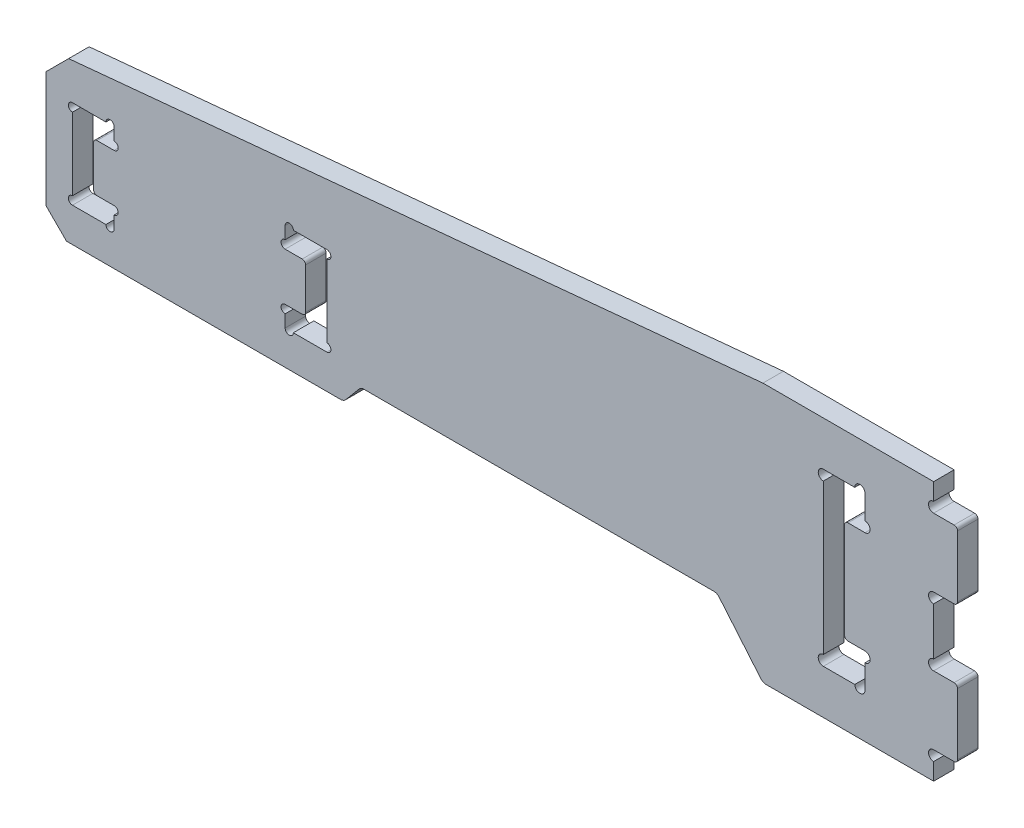
SolidWorks part; units mm, degrees
ref_plane "前视基准面" through (0, 0, 0) normal (0, 0, 1) x (1, 0, 0)
ref_plane "上视基准面" through (0, 0, 0) normal (0, 1, 0) x (1, 0, 0)
ref_plane "右视基准面" through (0, 0, 0) normal (1, 0, 0) x (0, 0, -1)
sketch "草图1" plane through (0, 0, 0) normal (0, 0, 1) x (1, 0, 0)
  line L1 (65, -19) -> (-65, -19)
  line L2 (65, -19) -> (65, 19)
  line L3 (65, 19) -> (-65, 19)
  line L4 (-65, -19) -> (-65, 19)
  line L5 (65, -19) -> (-65, 19) construction
  line L6 (65, 19) -> (-65, -19) construction
  point P0 (0, 0)
  dimension "D1" = 130
  dimension "D2" = 38
extrude "凸台-拉伸1" add sketch "草图1" along normal mid plane 3
sketch "草图2" plane through (0, 0, 1.5) normal (0, 0, 1) x (1, 0, 0)
  line L0 (65, -19) -> (65, 19) construction
  line L1 (68.5, 5) -> (65, 5)
  line L2 (68.5, 5) -> (68.5, 15)
  line L3 (68.5, 15) -> (65, 15)
  line L4 (65, 5) -> (65, 15)
  line L5 (68.5, 5) -> (65, 15) construction
  line L6 (68.5, 15) -> (65, 5) construction
  line L7 (66.75, 10) -> (66.75, -10) construction
  line L8 (68.5, -15) -> (65, -15)
  line L9 (68.5, -15) -> (68.5, -5)
  line L10 (68.5, -5) -> (65, -5)
  line L11 (65, -15) -> (65, -5)
  line L12 (68.5, -15) -> (65, -5) construction
  line L13 (68.5, -5) -> (65, -15) construction
  point P0 (66.75, 10)
  point P7 (66.75, -10)
  point P14 (66.75, 0)
  dimension "D1" = 20
  dimension "D2" = 3.5
  dimension "D3" = 10
extrude "凸台-拉伸2" add sketch "草图2" against normal blind 3
sketch "草图4" plane through (0, 0, 1.5) normal (0, 0, 1) x (1, 0, 0)
  line L0 (48.85, 12.5) -> (54.95, 12.5)
  line L1 (54.95, 12.5) -> (54.95, 7.5)
  line L2 (54.95, 7.5) -> (51.95, 7.5)
  line L3 (51.95, 7.5) -> (51.95, -7.5)
  line L4 (51.95, -7.5) -> (54.95, -7.5)
  line L5 (54.95, -7.5) -> (54.95, -12.5)
  line L6 (54.95, -12.5) -> (48.85, -12.5)
  line L7 (48.85, -12.5) -> (48.85, 12.5)
  line L9 (65, 15) -> (65, 19) construction
  point P8 (48.85, 0)
  dimension "D1" = 15
  dimension "D2" = 10.05
  dimension "D3" = 3
  dimension "D4" = 3.1
  dimension "D5" = 5
extrude "切除-拉伸2" cut sketch "草图4" against normal through all
sketch "草图3" plane through (0, 0, 1.5) normal (0, 0, 1) x (1, 0, 0)
  line L0 (65, 15) -> (65, 19) construction
  line L1 (65, -5) -> (65, 5) construction
  line L2 (65, -19) -> (65, -15) construction
  line L3 (54.95, 7.5) -> (54.95, 12.5) construction
  line L4 (54.95, 12.5) -> (48.85, 12.5) construction
  line L5 (48.85, 12.5) -> (48.85, -12.5) construction
  line L6 (54.95, -12.5) -> (54.95, -7.5) construction
  line L7 (48.85, -12.5) -> (54.95, -12.5) construction
  circle A0 centre (65, 15.75) radius 0.75
  circle A1 centre (65, 4.25) radius 0.75
  circle A2 centre (65, -4.25) radius 0.75
  circle A3 centre (65, -15.75) radius 0.75
  circle A4 centre (54.95, 8.25) radius 0.75
  circle A5 centre (54.2, 12.5) radius 0.75
  circle A6 centre (48.85, 11.75) radius 0.75
  circle A7 centre (48.85, -11.75) radius 0.75
  circle A8 centre (54.95, -8.25) radius 0.75
  circle A9 centre (54.2, -12.5) radius 0.75
  dimension "D1" = 1.5
extrude "切除-拉伸1" cut sketch "草图3" against normal through all
fillet "圆角1" radius 0.5 6 edges at (68.5, -5, 0) (68.5, -15, 0) (68.5, 15, 0) (68.5, 5, 0) (51.95, -7.5, 0) (51.95, 7.5, 0)
sketch "草图5" plane through (0, 0, 1.5) normal (0, 0, 1) x (1, 0, 0)
  line L1 (-65, 19) -> (-65, -19) construction
  line L6 (-65, -19) -> (-65, -14)
  line L7 (-65, -14) -> (35.8045, -14)
  line L8 (35.8045, -14) -> (40, -19)
  line L9 (-65, -19) -> (65, -19) construction
  line L10 (40, -19) -> (-65, -19)
  dimension "D4" = 5
  dimension "D5" = 105
  dimension "D6" = 50
extrude "切除-拉伸3" cut sketch "草图5" against normal through all
fillet "圆角2" radius 1 2 edges at (40, -19, 0) (35.8045, -14, 0)
sketch "草图6" plane through (0, 0, 1.5) normal (0, 0, 1) x (1, 0, 0)
  line L0 (-65, 9) -> (40, 19)
  line L1 (-65, 19) -> (-65, -14) construction
  line L2 (40, 19) -> (-65, 19)
  line L3 (-65, 19) -> (-65, 9)
  line L4 (65, 19) -> (-65, 19) construction
  dimension "D1" = 105
  dimension "D2" = 10
extrude "切除-拉伸4" cut sketch "草图6" against normal through all
sketch "草图8" plane through (0, 0, -1.5) normal (0, 0, -1) x (-1, 0, 0)
  line L0 (29.975, -6) -> (29.975, -9)
  line L1 (29.975, -9) -> (23.875, -9)
  line L2 (23.875, -9) -> (23.875, 4)
  line L3 (23.875, 4) -> (29.975, 4)
  line L4 (29.975, 4) -> (29.975, 1)
  line L5 (29.975, 1) -> (26.975, 1)
  line L6 (26.975, 1) -> (26.975, -6)
  line L7 (26.975, -6) -> (29.975, -6)
  line L8 (-65, 16.5) -> (-65, 19) construction
  line L11 (42.5, 4) -> (42.5, -9) construction
  line L12 (58.025, 1) -> (58.025, -6)
  line L13 (55.025, 1) -> (58.025, 1)
  line L14 (55.025, 4) -> (55.025, 1)
  line L15 (61.125, 4) -> (55.025, 4)
  line L16 (61.125, -9) -> (61.125, 4)
  line L17 (55.025, -9) -> (61.125, -9)
  line L18 (55.025, -6) -> (55.025, -9)
  line L19 (58.025, -6) -> (55.025, -6)
  line L20 (-51.95, -2.5) -> (42.5, -2.5) construction
  line L22 (-51.95, -7) -> (-51.95, 7) construction
  line L23 (-35.3382, -14) -> (65, -14) construction
  dimension "D1" = 107.5
  dimension "D2" = 7
  dimension "D3" = 3
  dimension "D4" = 3
  dimension "D5" = 3.1
  dimension "D6" = 11.5
  dimension "D7" = 25.05
extrude "切除-拉伸6" cut sketch "草图8" against normal through all
sketch "草图9" plane through (0, 0, -1.5) normal (0, 0, -1) x (-1, 0, 0)
  line L0 (29.975, 1) -> (29.975, 4) construction
  line L1 (29.975, -9) -> (29.975, -6) construction
  line L2 (23.875, -9) -> (29.975, -9) construction
  line L3 (29.975, 4) -> (23.875, 4) construction
  line L4 (23.875, 4) -> (23.875, -9) construction
  line L5 (55.025, -6) -> (55.025, -9) construction
  line L6 (55.025, -9) -> (61.125, -9) construction
  line L7 (55.025, 4) -> (55.025, 1) construction
  line L8 (61.125, 4) -> (55.025, 4) construction
  line L9 (61.125, -9) -> (61.125, 4) construction
  circle A0 centre (29.975, 1.6) radius 0.6
  circle A1 centre (29.975, -6.6) radius 0.6
  circle A2 centre (29.375, -9) radius 0.6
  circle A3 centre (29.375, 4) radius 0.6
  circle A4 centre (23.875, 3.4) radius 0.6
  circle A5 centre (23.875, -8.4) radius 0.6
  circle A6 centre (55.025, -6.6) radius 0.6
  circle A7 centre (55.625, -9) radius 0.6
  circle A8 centre (55.025, 1.6) radius 0.6
  circle A9 centre (55.625, 4) radius 0.6
  circle A10 centre (61.125, 3.4) radius 0.6
  circle A11 centre (61.125, -8.4) radius 0.6
  dimension "D1" = 1.2
extrude "切除-拉伸7" cut sketch "草图9" against normal through all
fillet "圆角3" radius 0.5 4 edges at (-26.975, 1, 0) (-26.975, -6, 0) (-58.025, 1, 0) (-58.025, -6, 0)
sketch "草图11" plane through (0, 0, -1.5) normal (0, 0, -1) x (-1, 0, 0)
  line L0 (21.3923, -14) -> (18.875, -11)
  line L1 (-35.3382, -14) -> (65, -14) construction
  line L2 (18.875, -11) -> (-33.2872, -11)
  line L3 (-33.2872, -11) -> (-36.1042, -14.3572)
  line L4 (-39.7003, -18.6428) -> (-36.1042, -14.3572) construction
  line L5 (-35.3382, -14) -> (21.3923, -14)
  line L8 (23.875, 2.8) -> (23.875, -7.8) construction
  arc A0 (-35.3382, -14) -> (-36.1042, -14.3572) centre (-35.3382, -15) ccw construction
  arc A1 (-35.3382, -14) -> (-36.1042, -14.3572) centre (-35.3382, -15) ccw
  dimension "D1" = 50
  dimension "D2" = 3
  dimension "D3" = 5
extrude "切除-拉伸8" cut sketch "草图11" against normal through all
fillet "圆角4" radius 1 3 edges at (-21.3923, -14, 0) (-18.875, -11, 0) (33.2872, -11, 0)
chamfer "倒角1" distance 3 angle 45 2 edges at (-65, 9, 0) (-65, -14, 0)
